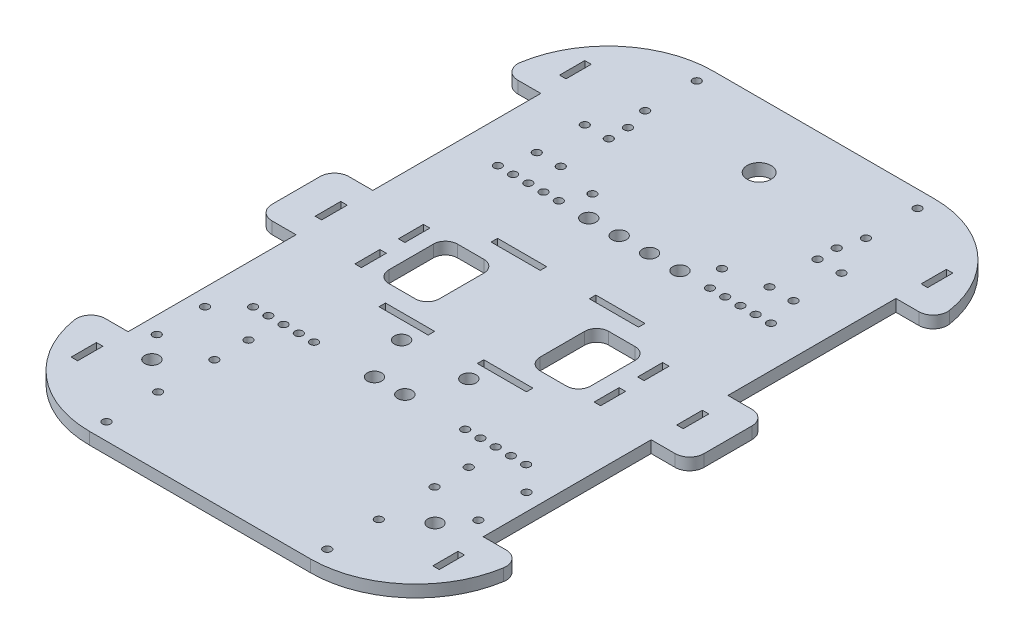
SolidWorks part; units mm, degrees
ref_plane "Ön Düzlem" through (0, 0, 0) normal (0, 0, 1) x (1, 0, 0)
ref_plane "Üst Düzlem" through (0, 0, 0) normal (0, 1, 0) x (1, 0, 0)
ref_plane "Sağ Düzlem" through (0, 0, 0) normal (1, 0, 0) x (0, 0, -1)
sketch "Sketch2" plane through (0, 0, 0) normal (0, 1, 0) x (1, 0, 0)
  line L0 (-74, -86) -> (-74, -51) construction
  line L1 (46, -130) -> (-46, -130)
  line L2 (90, -10) -> (90, 10)
  line L3 (46, 130) -> (-46, 130)
  line L4 (-90, -10) -> (-90, 10)
  line L5 (90, -130) -> (-90, 130) construction
  line L6 (90, 130) -> (-90, -130) construction
  line L7 (-83.5233, 86) -> (-74, 86)
  line L9 (-84, 16) -> (-74, 16)
  line L10 (-74, 86) -> (-74, 16)
  line L11 (-83.5233, -86) -> (-74, -86)
  line L13 (-84, -16) -> (-74, -16)
  line L14 (-74, -86) -> (-74, -16)
  line L15 (83.5233, 86) -> (74, 86)
  line L17 (84, 16) -> (74, 16)
  line L18 (74, 86) -> (74, 16)
  line L19 (83.5233, -86) -> (74, -86)
  line L21 (84, -16) -> (74, -16)
  line L22 (74, -86) -> (74, -16)
  line L23 (-74, 51) -> (74, 51) construction
  line L24 (-74, -51) -> (74, -51) construction
  line L26 (-74, 96.51) -> (-76.7, 96.51)
  line L27 (-76.7, 96.51) -> (-76.7, 107.02)
  line L28 (-74, 107.02) -> (-76.7, 107.02)
  line L29 (-74, 96.51) -> (-74, 107.02)
  line L30 (74, 96.51) -> (74, 107.02)
  line L31 (74, 107.02) -> (76.7, 107.02)
  line L32 (76.7, 96.51) -> (76.7, 107.02)
  line L33 (74, 96.51) -> (76.7, 96.51)
  line L34 (74, -107.02) -> (76.7, -107.02)
  line L35 (76.7, -96.51) -> (76.7, -107.02)
  line L36 (74, -96.51) -> (74, -107.02)
  line L37 (74, -96.51) -> (76.7, -96.51)
  line L38 (-74, -96.51) -> (-74, -107.02)
  line L39 (-74, -107.02) -> (-76.7, -107.02)
  line L40 (-76.7, -96.51) -> (-76.7, -107.02)
  line L41 (-74, -96.51) -> (-76.7, -96.51)
  line L42 (-74, 5.3333) -> (-74, -5.3333)
  line L43 (74, 5.3333) -> (74, -5.3333)
  line L44 (-74, 5.3333) -> (-76.7, 5.3333)
  line L45 (-76.7, 5.3333) -> (-76.7, -5.3333)
  line L46 (-76.7, -5.3333) -> (-74, -5.3333)
  line L47 (74, 5.3333) -> (76.7, 5.3333)
  line L48 (76.7, 5.3333) -> (76.7, -5.3333)
  line L49 (76.7, -5.3333) -> (74, -5.3333)
  arc A2 (-46, -130) -> (-89.4481, -92.9474) centre (-46, -86) cw
  arc A3 (-89.4481, 92.9474) -> (-46, 130) centre (-46, 86) cw
  arc A4 (89.4481, 92.9474) -> (46, 130) centre (46, 86) ccw
  arc A5 (89.4481, -92.9474) -> (46, -130) centre (46, -86) cw
  arc A6 (-84, 16) -> (-90, 10) centre (-84, 10) ccw
  arc A7 (-84, -16) -> (-90, -10) centre (-84, -10) cw
  arc A8 (90, 10) -> (84, 16) centre (84, 10) ccw
  arc A9 (90, -10) -> (84, -16) centre (84, -10) cw
  arc A10 (-89.4481, -92.9474) -> (-83.5233, -86) centre (-83.5233, -92) cw
  arc A11 (83.5233, -86) -> (89.4481, -92.9474) centre (83.5233, -92) cw
  arc A12 (-89.4481, 92.9474) -> (-83.5233, 86) centre (-83.5233, 92) ccw
  arc A13 (89.4481, 92.9474) -> (83.5233, 86) centre (83.5233, 92) cw
  point P0 (0, 0)
  point P34 (-90, -16)
  point P39 (90, -16)
  point P46 (-90, 86)
  point P49 (90, 86)
  dimension "D3" = 44
  dimension "D4" = 44
  dimension "D5" = 44
  dimension "D6" = 44
  dimension "D15" = 6
  dimension "D16" = 6
  dimension "D17" = 6
  dimension "D18" = 6
  dimension "D19" = 6
  dimension "D20" = 6
  dimension "D21" = 6
  dimension "D22" = 6
  dimension "D1" = 260
  dimension "D2" = 180
  dimension "D7" = 16
  dimension "D8" = 70
  dimension "D9" = 16
  dimension "D10" = 70
  dimension "D11" = 70
  dimension "D12" = 16
  dimension "D13" = 16
  dimension "D14" = 70
extrude "Boss-Extrude4" add sketch "Sketch2" along normal blind 5
sketch "Sketch5" plane through (0, 5, 0) normal (0, 1, 0) x (1, 0, 0)
  line L0 (-53.5, 63.83) -> (-43.5, 63.83) construction
  line L1 (-43.5, 63.83) -> (-43.5, 83.83) construction
  line L2 (-43.5, 83.83) -> (-43.5808, 83.8151) construction
  line L3 (-43.5808, 83.8151) -> (-53.5, 83.83) construction
  line L4 (-74, 86) -> (-74, 16) construction
  line L5 (53.5, 83.83) -> (43.5, 83.83) construction
  line L6 (43.5, 83.83) -> (43.5, 63.83) construction
  line L7 (43.5, 63.83) -> (53.5, 63.83) construction
  line L8 (74, 16) -> (74, 86) construction
  line L9 (46, 130) -> (-46, 130) construction
  line L12 (30.72, -24.7) -> (30.72, -22)
  line L19 (-30.72, -24.7) -> (-30.72, -22)
  line L20 (-30.72, -22) -> (-10.24, -22)
  line L22 (-10.24, -22) -> (-10.24, -24.7)
  line L26 (30.72, -22) -> (10.24, -22)
  line L27 (10.24, -22) -> (10.24, -24.7)
  line L32 (30.72, 24.7) -> (30.72, 22)
  line L33 (30.72, 22) -> (10.24, 22)
  line L34 (10.24, 22) -> (10.24, 24.7)
  line L35 (-30.72, 24.7) -> (-30.72, 22)
  line L36 (-30.72, 22) -> (-10.24, 22)
  line L37 (-10.24, 22) -> (-10.24, 24.7)
  line L41 (51.2, -14.28) -> (48.5, -14.28)
  line L42 (48.5, -14.28) -> (48.5, -3.86)
  line L43 (48.5, -3.86) -> (51.2, -3.86)
  line L47 (48.5, 3.86) -> (51.2, 3.86)
  line L48 (48.5, 14.28) -> (48.5, 3.86)
  line L49 (51.2, 14.28) -> (48.5, 14.28)
  line L53 (-51.2, 14.28) -> (-48.5, 14.28)
  line L54 (-48.5, 14.28) -> (-48.5, 3.86)
  line L55 (-48.5, 3.86) -> (-51.2, 3.86)
  line L56 (-48.5, -3.86) -> (-51.2, -3.86)
  line L57 (-48.5, -14.28) -> (-48.5, -3.86)
  line L58 (-51.2, -14.28) -> (-48.5, -14.28)
  line L61 (30.72, 24.7) -> (10.24, 24.7)
  line L63 (-10.24, 24.7) -> (-30.72, 24.7)
  line L65 (-10.24, -24.7) -> (-30.72, -24.7)
  line L66 (10.24, -24.7) -> (30.72, -24.7)
  line L68 (51.2, -14.28) -> (51.2, -3.86)
  line L70 (51.2, 14.28) -> (51.2, 3.86)
  line L71 (-51.2, -14.28) -> (-51.2, -3.86)
  line L72 (-51.2, 3.86) -> (-51.2, 14.28)
  line L75 (37.006, 14.28) -> (26.003, 14.28)
  line L76 (42.006, 9.28) -> (42.006, -9.28)
  line L77 (37.006, -14.28) -> (26.003, -14.28)
  line L78 (-42.006, 9.28) -> (-42.006, -9.28)
  line L79 (21.003, -7.14) -> (21.003, -9.28)
  line L82 (21.003, -7.14) -> (21.003, 9.28)
  line L85 (-26.003, 14.28) -> (-37.006, 14.28)
  line L86 (-26.003, -14.28) -> (-37.006, -14.28)
  line L88 (-21.003, -9.28) -> (-21.003, 9.28)
  circle A2 centre (-56.9, -51) radius 1.65
  circle A3 centre (-50.55, -51) radius 1.65
  circle A4 centre (-44.2, -51) radius 1.65
  circle A5 centre (-37.85, -51) radius 1.65
  circle A6 centre (-31.5, -51) radius 1.65
  circle A7 centre (31.5, -51) radius 1.65
  circle A8 centre (37.85, -51) radius 1.65
  circle A9 centre (44.2, -51) radius 1.65
  circle A10 centre (50.55, -51) radius 1.65
  circle A11 centre (56.9, -51) radius 1.65
  circle A16 centre (56.9, 51) radius 1.65
  circle A17 centre (50.55, 51) radius 1.65
  circle A18 centre (44.2, 51) radius 1.65
  circle A19 centre (37.85, 51) radius 1.65
  circle A20 centre (31.5, 51) radius 1.65
  circle A21 centre (-31.5, 51) radius 1.65
  circle A22 centre (-37.85, 51) radius 1.65
  circle A23 centre (-44.2, 51) radius 1.65
  circle A24 centre (-50.55, 51) radius 1.65
  circle A25 centre (-56.9, 51) radius 1.65
  circle A29 centre (-14, -32) radius 3
  circle A30 centre (14, -32) radius 3
  circle A31 centre (19, 51) radius 3
  circle A32 centre (-19, 51) radius 3
  circle A45 centre (-53.5, 83.83) radius 1.65
  circle A46 centre (-53.5, 63.83) radius 1.65
  circle A47 centre (-43.5, 63.83) radius 1.65
  circle A48 centre (-43.5, 83.83) radius 1.65
  circle A49 centre (43.5, 63.83) radius 1.65
  circle A50 centre (53.5, 63.83) radius 1.65
  circle A51 centre (43.5, 83.83) radius 1.65
  circle A52 centre (53.5, 83.83) radius 1.65
  circle A53 centre (-46, 123) radius 1.65
  circle A54 centre (-46, 101.5) radius 1.65
  circle A55 centre (46, 101.5) radius 1.65
  circle A56 centre (46, 123) radius 1.65
  circle A61 centre (-67, -60.96) radius 1.65
  circle A62 centre (-45.8971, -63.9231) radius 1.65
  circle A63 centre (-67, -81.04) radius 1.65
  circle A64 centre (-45.8971, -78.1568) radius 1.65
  circle A65 centre (45.8971, -63.9231) radius 1.65
  circle A66 centre (45.8971, -78.1568) radius 1.65
  circle A67 centre (67, -81.04) radius 1.65
  circle A68 centre (67, -60.96) radius 1.65
  circle A69 centre (46, -123) radius 1.65
  circle A70 centre (46, -101.5) radius 1.65
  circle A71 centre (-46, -101.5) radius 1.65
  circle A72 centre (-46, -123) radius 1.65
  circle A73 centre (-27, 60.5) radius 1.65
  circle A74 centre (27, 60.5) radius 1.65
  circle A75 centre (-43.5, 91.83) radius 1.65
  circle A76 centre (43.5, 91.83) radius 1.65
  circle A77 centre (-6.3333, 51) radius 3
  circle A78 centre (6.3333, 51) radius 3
  circle A79 centre (0, 103) radius 5
  circle A81 centre (59, -91.08) radius 3
  circle A82 centre (-59, -91.08) radius 3
  circle A83 centre (-6.3333, -51) radius 3
  circle A84 centre (6.3333, -51) radius 3
  arc A85 (-37.006, -14.28) -> (-42.006, -9.28) centre (-37.006, -9.28) cw
  arc A86 (-37.006, 14.28) -> (-42.006, 9.28) centre (-37.006, 9.28) ccw
  arc A87 (-21.003, -9.28) -> (-26.003, -14.28) centre (-26.003, -9.28) cw
  arc A88 (-26.003, 14.28) -> (-21.003, 9.28) centre (-26.003, 9.28) cw
  arc A93 (26.003, -14.28) -> (21.003, -9.28) centre (26.003, -9.28) cw
  arc A94 (26.003, 14.28) -> (21.003, 9.28) centre (26.003, 9.28) ccw
  arc A95 (37.006, -14.28) -> (42.006, -9.28) centre (37.006, -9.28) ccw
  arc A96 (37.006, 14.28) -> (42.006, 9.28) centre (37.006, 9.28) cw
  point P30 (6.3333, 51)
  point P32 (-6.3333, 51)
  point P59 (0, 0)
  point P94 (0, 0)
  point P96 (0, 0)
  point P184 (-21.003, -14.28)
  point P185 (-21.003, 14.28)
  dimension "D1" = 20.5
  dimension "D2" = 20.5
  dimension "D6" = 5
  dimension "D7" = 5
  dimension "D8" = 5
  dimension "D9" = 5
  dimension "D14" = 5
  dimension "D15" = 5
  dimension "D16" = 5
  dimension "D17" = 5
  dimension "D3" = 46.17
  dimension "D4" = 66.17
  dimension "D5" = 66.17
extrude "Cut-Extrude1" cut sketch "Sketch5" against normal through all
